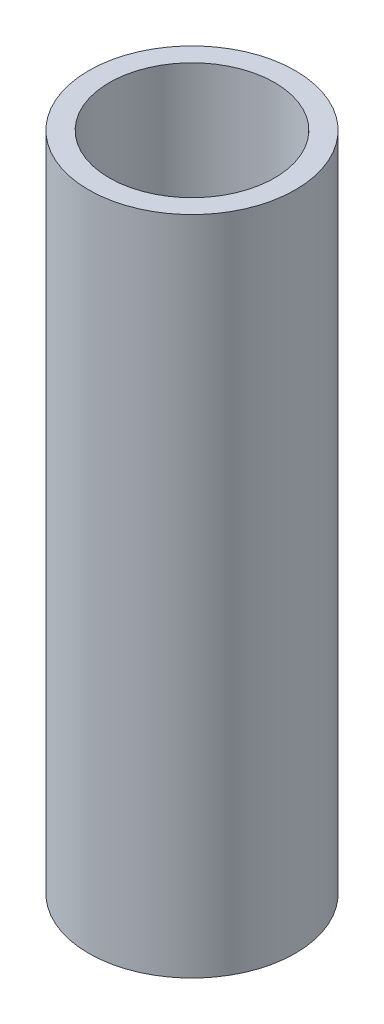
SolidWorks part; units mm, degrees
ref_plane "Alzado" through (0, 0, 0) normal (0, 0, 1) x (1, 0, 0)
ref_plane "Planta" through (0, 0, 0) normal (0, 1, 0) x (1, 0, 0)
ref_plane "Vista lateral" through (0, 0, 0) normal (1, 0, 0) x (0, 0, -1)
sketch "Croquis1" plane through (0, 0, 0) normal (0, 1, 0) x (1, 0, 0)
  circle A0 centre (0, 0) radius 12.5
  circle A1 centre (0, 0) radius 10
  dimension "D1" = 25
  dimension "D2" = 20
extrude "Saliente-Extruir1" add sketch "Croquis1" along normal mid plane 80
